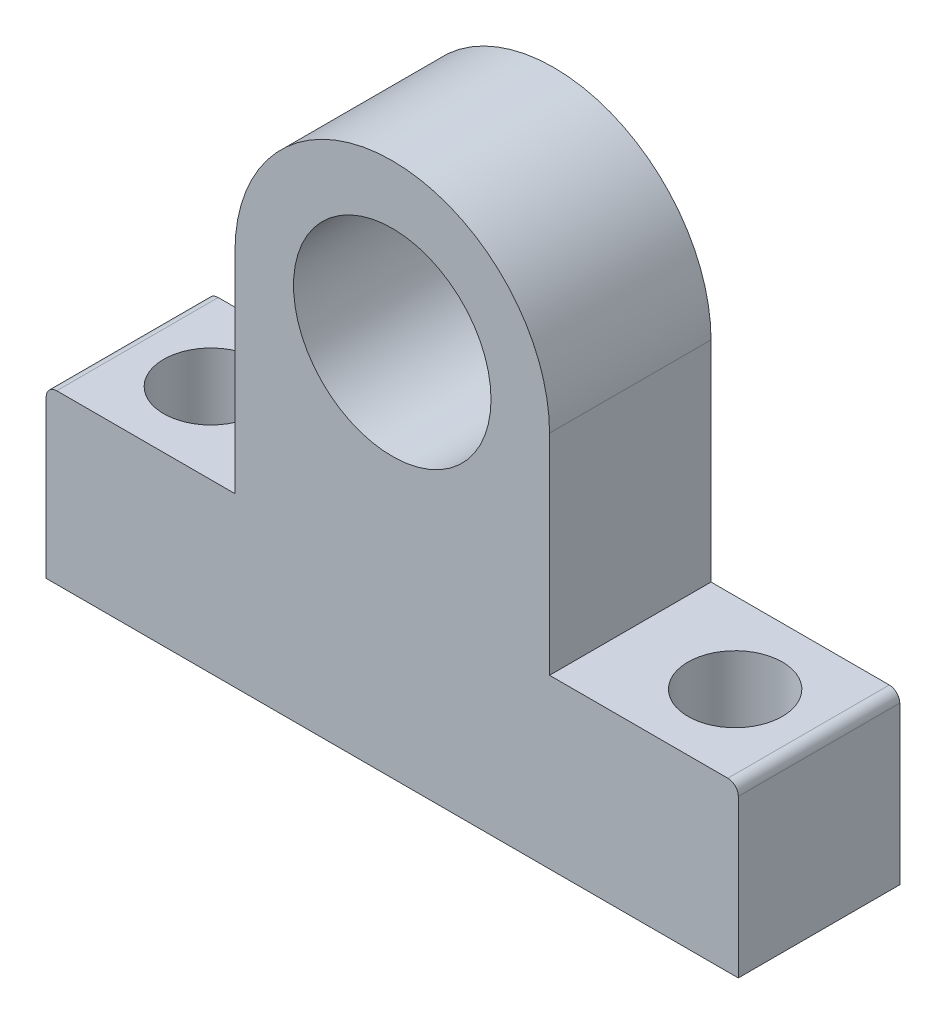
SolidWorks part; units mm, degrees
ref_plane "Alzado" through (0, 0, 0) normal (0, 0, 1) x (1, 0, 0)
ref_plane "Planta" through (0, 0, 0) normal (0, 1, 0) x (1, 0, 0)
ref_plane "Vista lateral" through (0, 0, 0) normal (1, 0, 0) x (0, 0, -1)
sketch "Croquis1" plane through (0, 0, 0) normal (0, 0, 1) x (1, 0, 0)
  line L0 (-41.6178, 0) -> (45.4013, 0) construction
  line L1 (-30.2675, 0) -> (-30.2675, 15)
  line L2 (-29.2675, 16) -> (-12.2675, 16)
  line L3 (-12.2675, 16) -> (-12.2675, 36)
  line L5 (17.7325, 36) -> (17.7325, 16)
  line L6 (17.7325, 16) -> (34.7325, 16)
  line L7 (35.7325, 15) -> (35.7325, 0)
  line L8 (-30.2675, 0) -> (35.7325, 0)
  arc A0 (17.7325, 36) -> (-12.2675, 36) centre (2.7325, 36) ccw
  arc A1 (34.7325, 16) -> (35.7325, 15) centre (34.7325, 15) cw
  arc A2 (-30.2675, 15) -> (-29.2675, 16) centre (-29.2675, 15) cw
  point P14 (35.7325, 16)
  point P17 (-30.2675, 16)
  dimension "D6" = 1
  dimension "D1" = 66
  dimension "D2" = 16
  dimension "D3" = 16
  dimension "D4" = 30
  dimension "D5" = 18
extrude "Saliente-Extruir1" add sketch "Croquis1" along normal blind 15.4
sketch "Croquis2" plane through (0, 0, 15.4) normal (0, 0, 1) x (1, 0, 0)
  line L0 (2.7325, 0) -> (2.7325, 52.3072) construction
  line L1 (-30.2675, 0) -> (35.7325, 0) construction
  circle A0 centre (2.7325, 36) radius 9.4179
  dimension "D1" = 36
extrude "Cortar-Extruir1" cut sketch "Croquis2" against normal through all
sketch "Croquis3" plane through (0, 0, 0) normal (0, -1, 0) x (1, 0, 0)
  line L0 (-30.2675, 7.7) -> (38.0395, 7.7) construction
  line L1 (-30.2675, 15.4) -> (-30.2675, 0) construction
  circle A0 centre (-22.2675, 7.7) radius 4.5
  circle A1 centre (27.7325, 7.7) radius 4.5
  dimension "D1" = 9
  dimension "D2" = 9
  dimension "D3" = 50
  dimension "D4" = 8
extrude "Cortar-Extruir2" cut sketch "Croquis3" against normal through all
equation "\"`9\"=7.09576"
